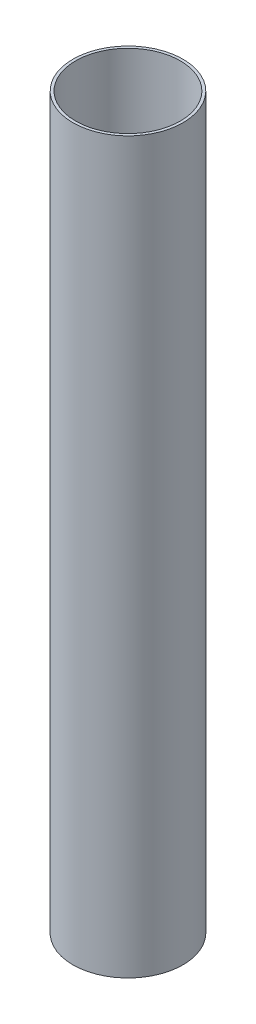
SolidWorks part; units mm, degrees
ref_plane "Plan de face" through (0, 0, 0) normal (0, 0, 1) x (1, 0, 0)
ref_plane "Plan de dessus" through (0, 0, 0) normal (0, 1, 0) x (1, 0, 0)
ref_plane "Plan de droite" through (0, 0, 0) normal (1, 0, 0) x (0, 0, -1)
sketch "Esquisse1" plane through (0, 0, 0) normal (0, 1, 0) x (1, 0, 0)
  circle A0 centre (0, 0) radius 20
  circle A1 centre (0, 0) radius 19
extrude "Boss.-Extru.1" add sketch "Esquisse1" along normal blind 265
